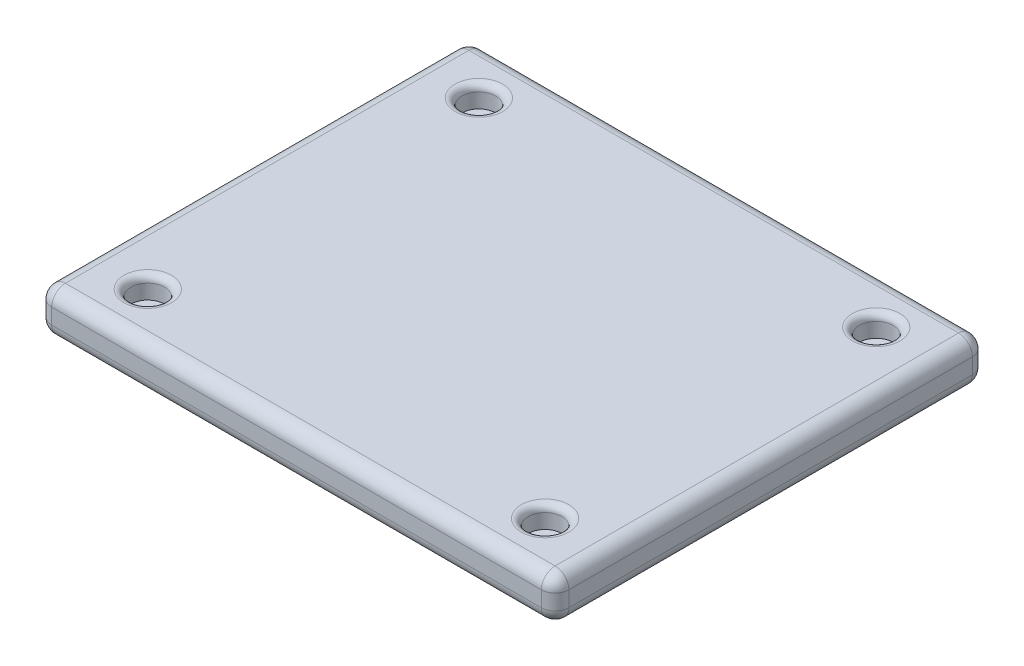
SolidWorks part; units mm, degrees
material "Teak"
ref_plane "Front Plane" through (0, 0, 0) normal (0, 0, 1) x (1, 0, 0)
ref_plane "Top Plane" through (0, 0, 0) normal (0, 1, 0) x (1, 0, 0)
ref_plane "Right Plane" through (0, 0, 0) normal (1, 0, 0) x (0, 0, -1)
sketch "Sketch1" plane through (0, 0, 0) normal (0, 1, 0) x (1, 0, 0)
  line L1 (300, 250) -> (-300, 250)
  line L2 (300, 250) -> (300, -250)
  line L3 (300, -250) -> (-300, -250)
  line L4 (-300, 250) -> (-300, -250)
  line L5 (300, 250) -> (-300, -250) construction
  line L6 (300, -250) -> (-300, 250) construction
  point P0 (0, 0)
  dimension "D1" = 600
  dimension "D2" = 500
extrude "Boss-Extrude1" add sketch "Sketch1" along normal blind 50
sketch "Sketch2" plane through (0, 50, 0) normal (0, 1, 0) x (1, 0, 0)
  circle A5 centre (-230.4664, -192.0553) radius 19.6
  circle A6 centre (230.4664, 192.0553) radius 19.6
  circle A7 centre (230.4664, -192.0553) radius 19.6
  circle A8 centre (-230.4664, 192.0553) radius 19.6
  point P0 (0, 0)
  point P5 (0, 0)
  point P8 (0, 0)
  point P13 (0, 0)
  dimension "D1" = 300
  dimension "D2" = 2
  dimension "D3" = 300
  dimension "D4" = 300
  dimension "D5" = 300
extrude "Cut-Extrude1" cut sketch "Sketch2" against normal blind 25
scale "Scale1" scale about centroid uniform scaling yes scale factor 0.125
fillet "Fillet4" radius 1 4 edges at (-28.8083, 28.0363, 26.4569) (28.8083, 28.0363, 21.5569) (28.8083, 28.0363, -21.5569) (-28.8083, 28.0363, -26.4569)
ref_plane "Plane3" through (0, 24.9113, 0) normal (0, 1, 0) x (1, 0, 0)
fillet "Fillet7" radius 2 12 edges at (-37.5, 28.0363, 0) (-37.5, 21.7863, 0) (-37.5, 24.9113, 31.25) (0, 28.0363, 31.25) (0, 21.7863, 31.25) (37.5, 24.9113, 31.25) (37.5, 28.0363, 0) (37.5, 21.7863, 0) (37.5, 24.9113, -31.25) (0, 28.0363, -31.25) (-37.5, 24.9113, -31.25) (0, 21.7863, -31.25)
